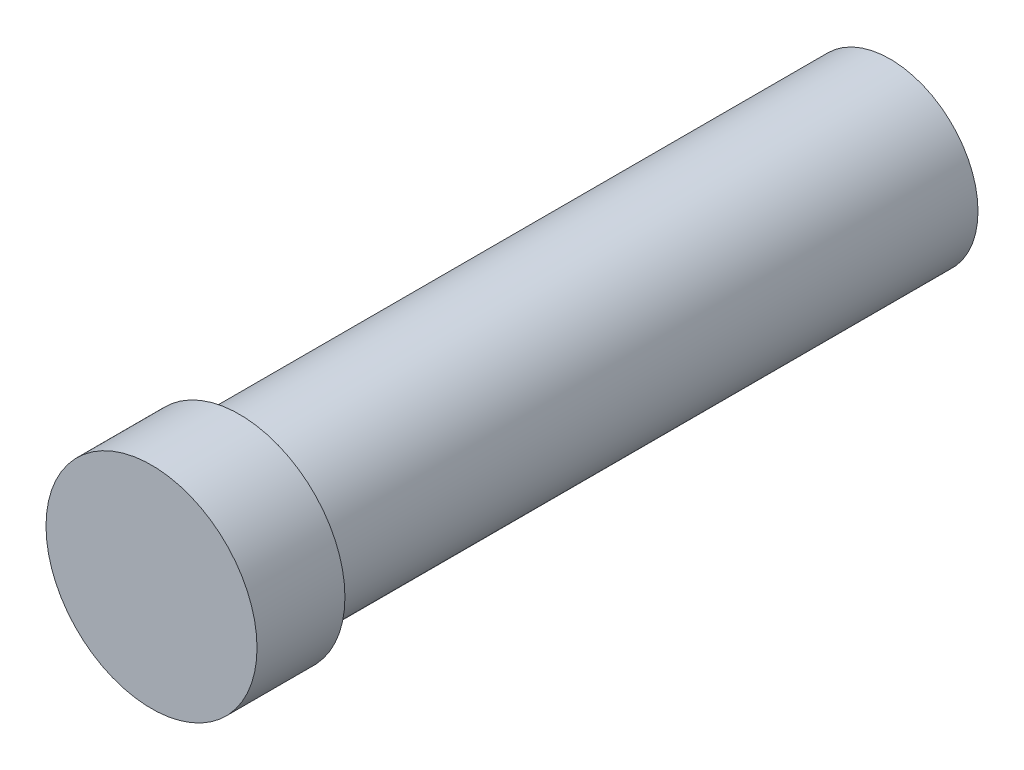
SolidWorks part; units mm, degrees
ref_plane "Front Plane" through (0, 0, 0) normal (0, 0, 1) x (1, 0, 0)
ref_plane "Top Plane" through (0, 0, 0) normal (0, 1, 0) x (1, 0, 0)
ref_plane "Right Plane" through (0, 0, 0) normal (1, 0, 0) x (0, 0, -1)
sketch "Sketch1" plane through (0, 0, 0) normal (0, 0, 1) x (1, 0, 0)
  circle A0 centre (0, 0) radius 5
  dimension "D1" = 10
extrude "Boss-Extrude1" add sketch "Sketch1" along normal blind 37
sketch "Sketch2" plane through (0, 0, 37) normal (0, 0, 1) x (1, 0, 0)
  circle A0 centre (0, 0) radius 6
  dimension "D1" = 12
extrude "Boss-Extrude2" add sketch "Sketch2" along normal blind 5
